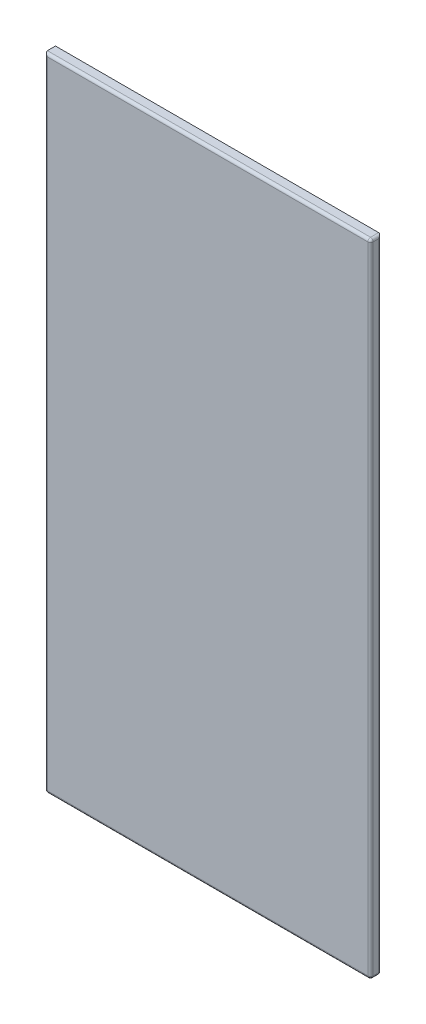
SolidWorks part; units mm, degrees
material "1060 Alloy"
ref_plane "Front Plane" through (0, 0, 0) normal (0, 0, 1) x (1, 0, 0)
ref_plane "Top Plane" through (0, 0, 0) normal (0, 1, 0) x (1, 0, 0)
ref_plane "Right Plane" through (0, 0, 0) normal (1, 0, 0) x (0, 0, -1)
sketch "Sketch1" plane through (0, 0, 0) normal (0, 0, 1) x (1, 0, 0)
  line L1 (-302.5, 595) -> (302.5, 595)
  line L2 (-302.5, 595) -> (-302.5, -595)
  line L3 (-302.5, -595) -> (302.5, -595)
  line L4 (302.5, 595) -> (302.5, -595)
  line L5 (-302.5, 595) -> (302.5, -595) construction
  line L6 (-302.5, -595) -> (302.5, 595) construction
  point P0 (0, 0)
  dimension "D1" = 605
  dimension "D2" = 1190
extrude "Boss-Extrude1" add sketch "Sketch1" along normal blind 20
fillet "Fillet1" radius 5 9 edges at (302.5, 0, 0) (0, -595, 0) (302.5, 0, 20) (0, 595, 20) (-302.5, 0, 20) (0, -595, 20) (302.5, -595, 10) (-302.5, -595, 10) (302.5, 595, 10)
